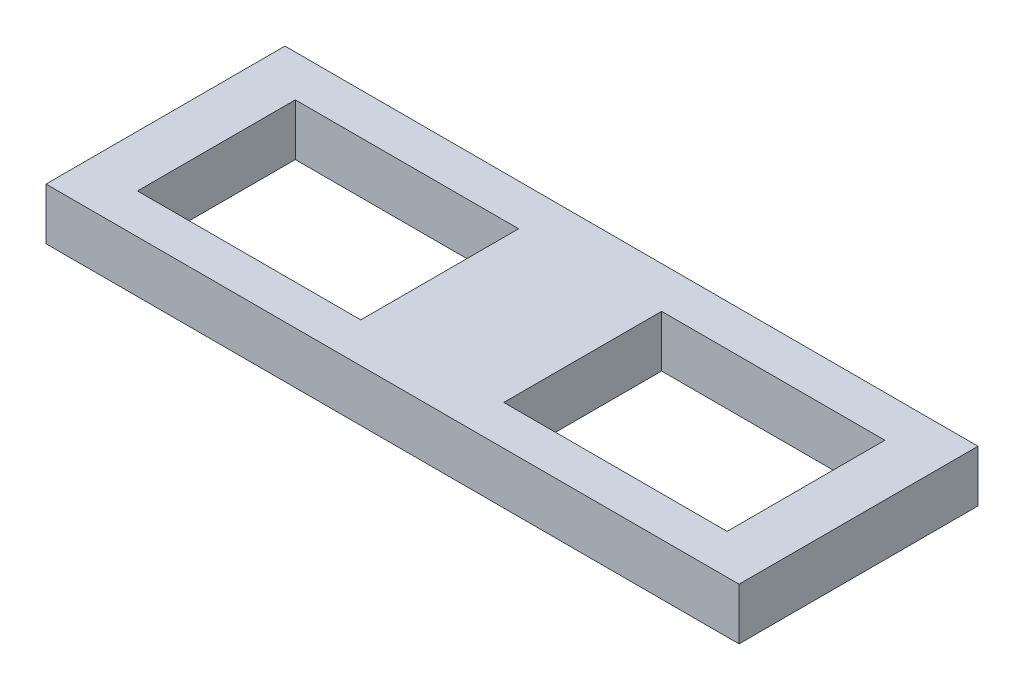
SolidWorks part; units mm, degrees
ref_plane "Alzado" through (0, 0, 0) normal (0, 0, 1) x (1, 0, 0)
ref_plane "Planta" through (0, 0, 0) normal (0, 1, 0) x (1, 0, 0)
ref_plane "Vista lateral" through (0, 0, 0) normal (1, 0, 0) x (0, 0, -1)
sketch "Croquis1" plane through (0, 0, 0) normal (0, 1, 0) x (1, 0, 0)
  line L0 (67, 46.2) -> (67, 0) construction
  line L1 (0, 0) -> (134, 0)
  line L2 (0, 0) -> (0, 46.2)
  line L3 (0, 46.2) -> (134, 46.2)
  line L4 (134, 0) -> (134, 46.2)
  line L5 (10, 38.2) -> (53.1777, 38.2)
  line L6 (10, 38.2) -> (10, 7.6861)
  line L7 (10, 7.6861) -> (53.1777, 7.6861)
  line L8 (53.1777, 38.2) -> (53.1777, 7.6861)
  line L9 (124, 7.6861) -> (80.8223, 7.6861)
  line L10 (80.8223, 38.2) -> (80.8223, 7.6861)
  line L11 (124, 38.2) -> (80.8223, 38.2)
  line L12 (124, 38.2) -> (124, 7.6861)
  dimension "D1" = 46.2
  dimension "D2" = 134
extrude "Saliente-Extruir2" add sketch "Croquis1" along normal blind 10
